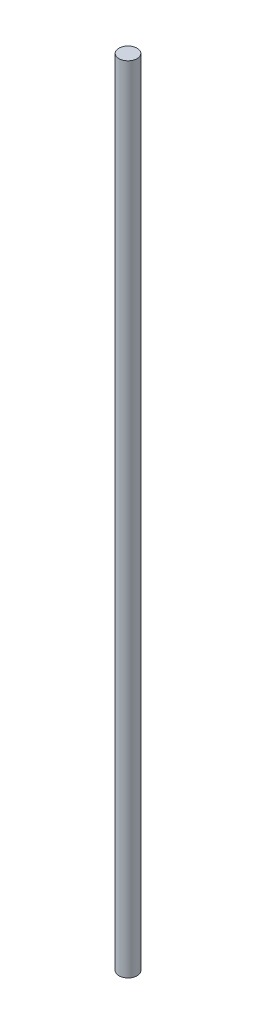
SolidWorks part; units mm, degrees
ref_plane "Front Plane" through (0, 0, 0) normal (0, 0, 1) x (1, 0, 0)
ref_plane "Top Plane" through (0, 0, 0) normal (0, 1, 0) x (1, 0, 0)
ref_plane "Right Plane" through (0, 0, 0) normal (1, 0, 0) x (0, 0, -1)
sketch "Sketch1" plane through (0, 0, 0) normal (0, 0, 1) x (1, 0, 0)
  line L0 (4, 350) -> (0, 350)
  line L1 (0, 350) -> (0, 0)
  line L2 (0, 0) -> (4, 0)
  line L3 (4, 0) -> (4, 350)
  line L4 (0, 350) -> (0, 0) construction
revolve "Revolve1" add sketch "Sketch1" angle 360 about L4
